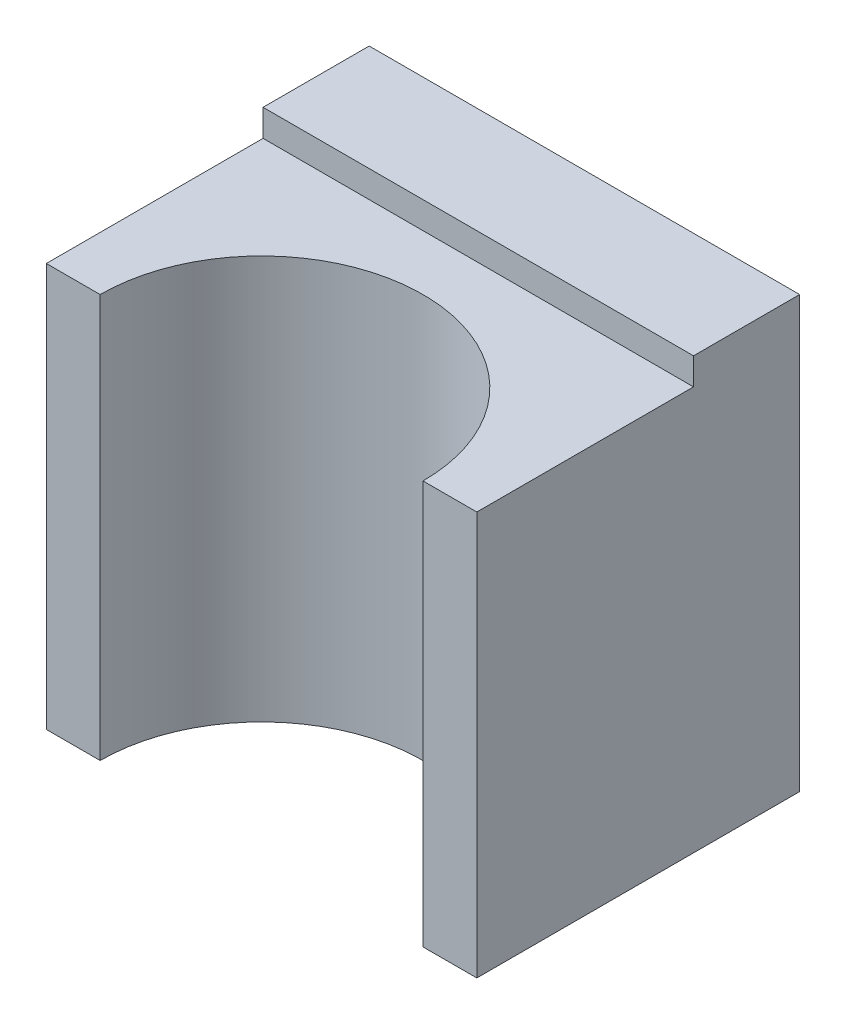
SolidWorks part; units mm, degrees
ref_plane "Front Plane" through (0, 0, 0) normal (0, 0, 1) x (1, 0, 0)
ref_plane "Top Plane" through (0, 0, 0) normal (0, 1, 0) x (1, 0, 0)
ref_plane "Right Plane" through (0, 0, 0) normal (1, 0, 0) x (0, 0, -1)
sketch "Sketch1" plane through (0, 0, 0) normal (0, 0, 1) x (1, 0, 0)
  line L0 (-50, 5) -> (-50, 45)
  line L1 (-50, 45) -> (-10, 45)
  line L2 (-10, 45) -> (-10, 5)
  line L3 (-10, 5) -> (-50, 5)
extrude "Boss-Extrude1" add sketch "Sketch1" along normal blind 30
sketch "Sketch2" plane through (0, 5, 0) normal (0, -1, 0) x (1, 0, 0)
  line L0 (-50, 30) -> (-10, 30) construction
  circle A0 centre (-30, 30) radius 15
  dimension "D1" = 30
extrude "Cut-Extrude1" cut sketch "Sketch2" against normal through all
sketch "Sketch3" plane through (0, 45, 0) normal (0, 1, 0) x (1, 0, 0)
  line L0 (-10, -30) -> (-15, -30)
  line L1 (-45, -30) -> (-50, -30)
  line L2 (-50, -30) -> (-50, -9.8625)
  line L3 (-50, -30) -> (-50, 0) construction
  line L4 (-50, -9.8625) -> (-10, -9.8625)
  line L5 (-10, -30) -> (-10, 0) construction
  line L6 (-10, -9.8625) -> (-10, -30)
  arc A0 (-45, -30) -> (-15, -30) centre (-30, -30) cw
  arc A1 (-15, -30) -> (-45, -30) centre (-30, -30) ccw construction
extrude "Cut-Extrude2" cut sketch "Sketch3" against normal blind 2.5
